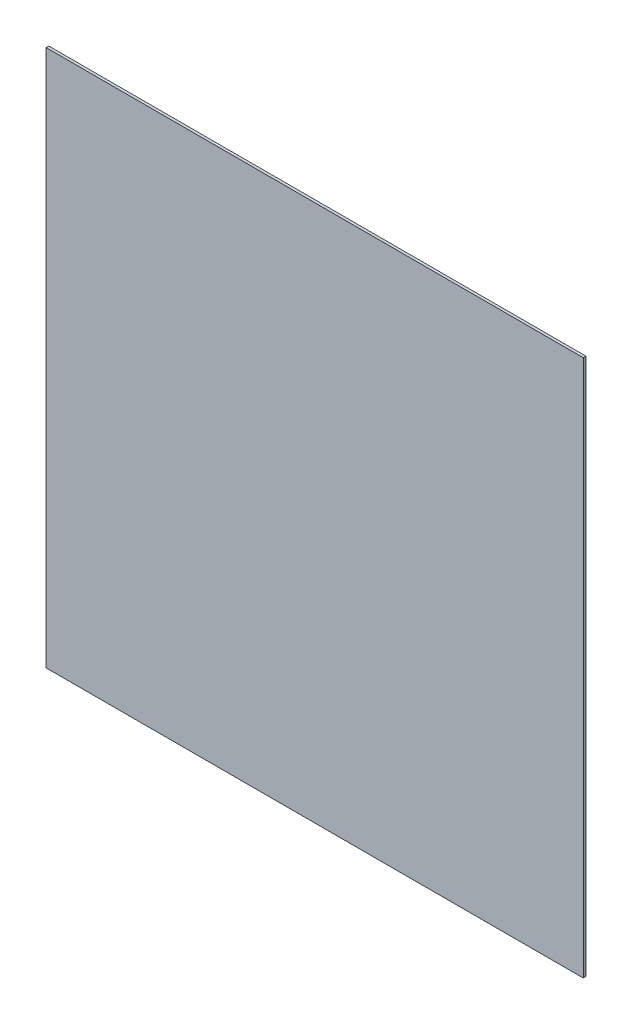
SolidWorks part; units mm, degrees
ref_plane "前视基准面" through (0, 0, 0) normal (0, 0, 1) x (1, 0, 0)
ref_plane "上视基准面" through (0, 0, 0) normal (0, 1, 0) x (1, 0, 0)
ref_plane "右视基准面" through (0, 0, 0) normal (1, 0, 0) x (0, 0, -1)
sketch "草图1" plane through (0, 0, 0) normal (0, 0, 1) x (1, 0, 0)
  line L0 (-100, 100) -> (100, 100)
  line L1 (-100, 100) -> (-100, -100)
  line L2 (100, 100) -> (100, -100)
  line L3 (-100, -100) -> (100, -100)
  line L4 (-100, 100) -> (100, -100) construction
  line L5 (100, 100) -> (-100, -100) construction
  point P1 (0, 0)
extrude "凸台-拉伸1" add sketch "草图1" along normal blind 1
